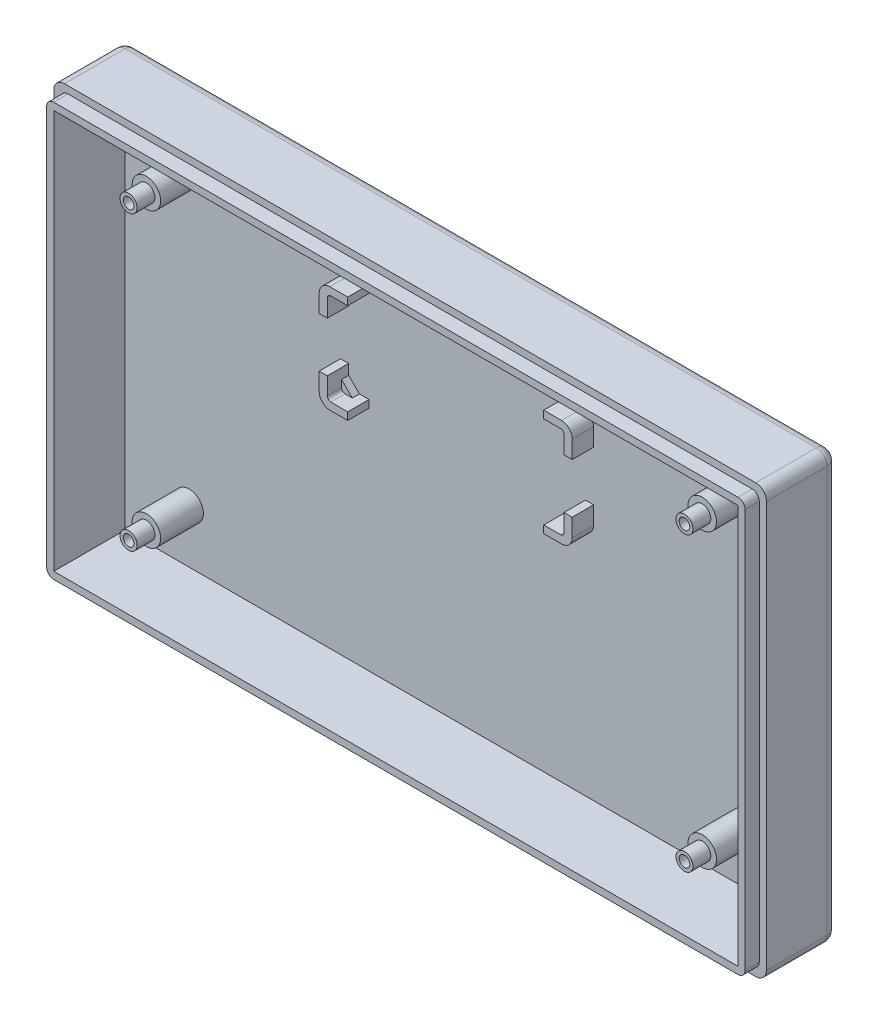
SolidWorks part; units mm, degrees
ref_plane "Front Plane" through (0, 0, 0) normal (0, 0, 1) x (1, 0, 0)
ref_plane "Top Plane" through (0, 0, 0) normal (0, 1, 0) x (1, 0, 0)
ref_plane "Right Plane" through (0, 0, 0) normal (1, 0, 0) x (0, 0, -1)
sketch "草图1" plane through (0, 0, 0) normal (0, 0, 1) x (1, 0, 0)
  line L1 (50, -30) -> (-50, -30)
  line L2 (50, -30) -> (50, 30)
  line L3 (50, 30) -> (-50, 30)
  line L4 (-50, -30) -> (-50, 30)
  line L5 (50, -30) -> (-50, 30) construction
  line L6 (50, 30) -> (-50, -30) construction
  point P0 (0, 0)
  dimension "D1" = 100
  dimension "D2" = 60
extrude "凸台-拉伸1" add sketch "草图1" along normal blind 2
sketch "草图2" plane through (0, 0, 2) normal (0, 0, 1) x (1, 0, 0)
  line L0 (50, -30) -> (50, 30) construction
  line L1 (-50, 30) -> (50, 30)
  line L2 (-50, 30) -> (-50, 27)
  line L3 (-48, 28) -> (48, 28)
  line L4 (50, 30) -> (50, 27)
  line L5 (-50, -30) -> (50, -30) construction
  line L6 (50, 30) -> (47, 30)
  line L7 (50, 30) -> (50, -30)
  line L8 (50, -30) -> (47, -30)
  line L9 (48, 28) -> (48, -28)
  line L10 (-50, 30) -> (-50, -30) construction
  line L11 (50, -30) -> (-50, -30)
  line L12 (50, -30) -> (50, -27)
  line L13 (48, -28) -> (-48, -28)
  line L14 (-50, -30) -> (-50, -27)
  line L15 (-50, 27) -> (-50, -27)
  line L16 (-50, 30) -> (-47, 30)
  line L17 (-50, 30) -> (-50, -30)
  line L18 (-50, -30) -> (-47, -30)
  line L19 (-48, 28) -> (-48, -28)
  line L20 (50, 27) -> (50, -27)
  line M9 (-50, 30) -> (-50, -30)
  line M10 (-50, -30) -> (50, -30)
  line M11 (50, -30) -> (50, 30)
  line M12 (50, 30) -> (-50, 30)
  dimension "D1" = 2
  dimension "D2" = 2
  dimension "D3" = 2
  dimension "D4" = 2
extrude "凸台-拉伸2" add sketch "草图2" along normal blind 10 contours L1 L11 L7 L19 L3 L9 L13 M12 M9 M10 M11
sketch "草图3" plane through (0, 0, 12) normal (0, 0, 1) x (1, 0, 0)
  line L1 (-50, 30) -> (50, 30)
  line L2 (-50, 30) -> (-50, -30)
  line L3 (-50, -30) -> (50, -30)
  line L4 (50, 30) -> (50, -30)
  line L5 (-49, 29) -> (49, 29)
  line L6 (-49, 29) -> (-49, -29)
  line L7 (-49, -29) -> (49, -29)
  line L8 (49, 29) -> (49, -29)
  dimension "D1" = 1
  dimension "D2" = 1
  dimension "D3" = 1
  dimension "D4" = 1
extrude "切除-拉伸1" cut sketch "草图3" against normal blind 2
sketch "草图4" plane through (0, 0, 2) normal (0, 0, 1) x (1, 0, 0)
  line L0 (0, 33.105) -> (0, -35.2648) construction
  line L1 (-52.2083, 0) -> (61.7413, 0) construction
  line L2 (-16.61, 11.45) -> (26.8293, 11.45) construction
  line L3 (-16.61, 17.9) -> (-13.75, 17.9)
  line L4 (-16.61, 17.9) -> (-16.61, 14.95)
  line L5 (-16.61, 5) -> (-13.75, 5)
  line L6 (16.61, 17.9) -> (16.61, 14.95)
  line L7 (-13.75, 18.95) -> (-13.75, 17.9)
  line L8 (17.75, 3.95) -> (13.75, 3.95)
  line L9 (17.75, 3.95) -> (17.75, 7.95)
  line L10 (17.75, 18.95) -> (13.75, 18.95)
  line L11 (-17.75, 3.95) -> (-17.75, 7.95)
  line L12 (17.75, 3.95) -> (-17.75, 18.95) construction
  line L13 (17.75, 18.95) -> (-17.75, 3.95) construction
  line L14 (-17.75, 14.95) -> (-16.61, 14.95)
  line L15 (13.75, 18.95) -> (13.75, 17.9)
  line L16 (17.75, 14.95) -> (16.61, 14.95)
  line L17 (17.75, 7.95) -> (16.61, 7.95)
  line L18 (13.75, 3.95) -> (13.75, 5)
  line L19 (-17.75, 7.95) -> (-16.61, 7.95)
  line L20 (-13.75, 3.95) -> (-13.75, 5)
  line L21 (-13.75, 18.95) -> (-17.75, 18.95)
  line L22 (13.75, 17.9) -> (16.61, 17.9)
  line L23 (17.75, 14.95) -> (17.75, 18.95)
  line L24 (16.61, 7.95) -> (16.61, 5)
  line L25 (13.75, 5) -> (16.61, 5)
  line L26 (-13.75, 3.95) -> (-17.75, 3.95)
  line L27 (-16.61, 7.95) -> (-16.61, 5)
  line L28 (-17.75, 14.95) -> (-17.75, 18.95)
  point P12 (0, 11.45)
  dimension "D1" = 33.22
  dimension "D2" = 12.9
  dimension "D3" = 5
  dimension "D4" = 35.5
  dimension "D5" = 15
  dimension "D6" = 4
  dimension "D7" = 4
extrude "凸台-拉伸3" add sketch "草图4" along normal blind 3
sketch "草图5" plane through (0, 0, 2) normal (0, 0, 1) x (1, 0, 0)
  line L0 (-16.61, 17.9) -> (-15.11, 17.9)
  line L1 (-16.61, 17.9) -> (-13.75, 17.9) construction
  line L2 (-15.11, 17.9) -> (-16.61, 16.4)
  line L3 (-16.61, 14.95) -> (-16.61, 17.9) construction
  line L4 (-16.61, 16.4) -> (-16.61, 17.9)
  line L5 (16.61, 17.9) -> (15.11, 17.9)
  line L6 (13.75, 17.9) -> (16.61, 17.9) construction
  line L7 (15.11, 17.9) -> (16.61, 16.4)
  line L8 (16.61, 17.9) -> (16.61, 14.95) construction
  line L9 (16.61, 16.4) -> (16.61, 17.9)
  line L10 (16.61, 5) -> (16.61, 6.5)
  line L11 (16.61, 7.95) -> (16.61, 5) construction
  line L12 (16.61, 6.5) -> (15.11, 5)
  line L13 (16.61, 5) -> (13.75, 5) construction
  line L14 (15.11, 5) -> (16.61, 5)
  line L15 (-16.61, 5) -> (-15.11, 5)
  line L16 (-13.75, 5) -> (-16.61, 5) construction
  line L17 (-15.11, 5) -> (-16.61, 6.5)
  line L18 (-16.61, 5) -> (-16.61, 7.95) construction
  line L19 (-16.61, 6.5) -> (-16.61, 5)
  dimension "D1" = 1.5
  dimension "D2" = 1.5
  dimension "D3" = 1.5
  dimension "D4" = 1.5
  dimension "D5" = 1.5
  dimension "D6" = 1.5
  dimension "D7" = 1.5
  dimension "D8" = 1.5
extrude "凸台-拉伸4" add sketch "草图5" along normal blind 1
fillet "圆角1" radius 0.5 4 edges at (16.61, 5, 4) (16.61, 17.9, 4) (-16.61, 5, 4) (-16.61, 17.9, 4)
fillet "圆角2" radius 1.5 4 edges at (17.75, 18.95, 3.5) (17.75, 3.95, 3.5) (-17.75, 3.95, 3.5) (-17.75, 18.95, 3.5)
sketch "草图6" plane through (0, 0, 2) normal (0, 0, 1) x (1, 0, 0)
  line L1 (39, -20.5) -> (-39, -20.5) construction
  line L2 (39, -20.5) -> (39, 20.5) construction
  line L3 (39, 20.5) -> (-39, 20.5) construction
  line L4 (-39, -20.5) -> (-39, 20.5) construction
  line L5 (39, -20.5) -> (-39, 20.5) construction
  line L6 (39, 20.5) -> (-39, -20.5) construction
  circle A0 centre (-39, 20.5) radius 2
  circle A1 centre (39, 20.5) radius 2
  circle A2 centre (39, -20.5) radius 2
  circle A3 centre (-39, -20.5) radius 2
  point P0 (0, 0)
  dimension "D3" = 4
  dimension "D4" = 4
  dimension "D5" = 4
  dimension "D6" = 4
  dimension "D1" = 78
  dimension "D2" = 41
extrude "凸台-拉伸5" add sketch "草图6" along normal blind 6
sketch "草图7" plane through (0, 0, 8) normal (0, 0, 1) x (1, 0, 0)
  circle A0 centre (-39, 20.5) radius 1.2
  circle A1 centre (39, 20.5) radius 1.2
  circle A2 centre (39, -20.5) radius 1.2
  circle A3 centre (-39, -20.5) radius 1.2
  dimension "D1" = 2.4
  dimension "D2" = 2.4
  dimension "D3" = 2.4
  dimension "D4" = 2.4
extrude "凸台-拉伸6" add sketch "草图7" along normal blind 2.5
sketch "草图8" plane through (0, 0, 10.5) normal (0, 0, 1) x (1, 0, 0)
  circle A0 centre (-39, 20.5) radius 0.75
  circle A1 centre (-39, -20.5) radius 0.75
  circle A2 centre (39, -20.5) radius 0.75
  circle A3 centre (39, 20.5) radius 0.75
  dimension "D1" = 1.5
  dimension "D2" = 1.5
  dimension "D3" = 1.5
  dimension "D4" = 1.5
extrude "切除-拉伸2" cut sketch "草图8" against normal blind 12.5
fillet "圆角3" radius 1.5 4 edges at (50, 30, 5) (50, -30, 5) (-50, -30, 5) (-50, 30, 5)
fillet "圆角4" radius 1.5 8 edges at (49.5607, -29.5607, 0) (-49.5607, -29.5607, 0) (-49.5607, 29.5607, 0) (49.5607, 29.5607, 0) (-50, 0, 0) (0, -30, 0) (0, 30, 0) (50, 0, 0)
fillet "圆角5" radius 1 4 edges at (49, 29, 11) (-49, 29, 11) (-49, -29, 11) (49, -29, 11)
sketch "草图9" plane through (0, 0, 0) normal (0, 0, -1) x (-1, 0, 0)
  circle A0 centre (-39, 20.5) radius 1.5
  dimension "D1" = 3
extrude "切除-拉伸3" cut sketch "草图9" against normal blind 7
pattern_linear "阵列(线性)1" count 2 spacing 78 along (-1, 0, 0) count 2 spacing 41 along (0, -1, 0) of "切除-拉伸3"
